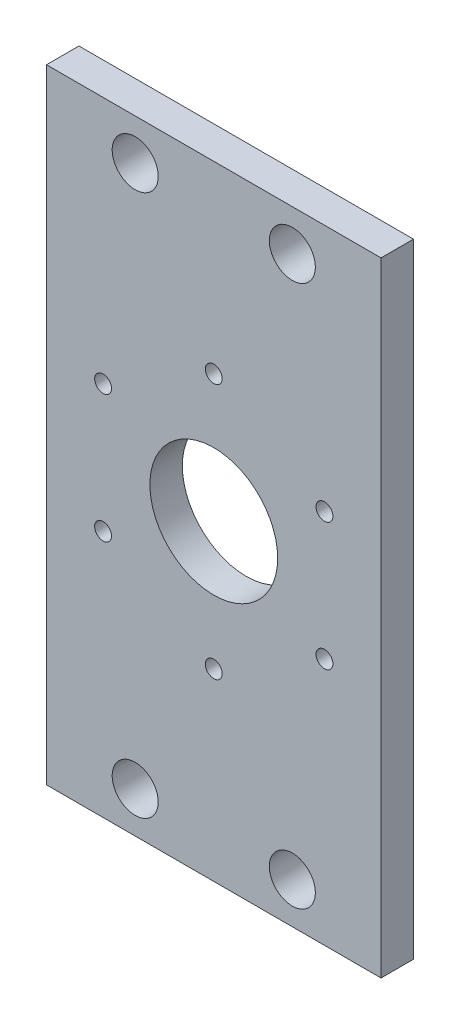
SolidWorks part; units mm, degrees
material "6061 Alloy"
ref_plane "Front Plane" through (0, 0, 0) normal (0, 0, 1) x (1, 0, 0)
ref_plane "Top Plane" through (0, 0, 0) normal (0, 1, 0) x (1, 0, 0)
ref_plane "Right Plane" through (0, 0, 0) normal (1, 0, 0) x (0, 0, -1)
sketch "Sketch1" plane through (0, 0, 0) normal (0, 0, 1) x (1, 0, 0)
  line L1 (-32.72, -61) -> (32.72, -61)
  line L2 (-32.72, -61) -> (-32.72, 61)
  line L3 (-32.72, 61) -> (32.72, 61)
  line L4 (32.72, -61) -> (32.72, 61)
  line L5 (-32.72, -61) -> (32.72, 61) construction
  line L6 (-32.72, 61) -> (32.72, -61) construction
  point P0 (0, 0)
  dimension "D1" = 122
  dimension "D2" = 65.44
extrude "Boss-Extrude1" add sketch "Sketch1" along normal blind 6.35
sketch "Sketch2" plane through (0, 0, 6.35) normal (0, 0, 1) x (1, 0, 0)
  line L0 (0, 0) -> (32.72, 0) construction
  line L1 (32.72, -61) -> (32.72, 61) construction
  line L2 (0, 0) -> (0, 61) construction
  line L3 (32.72, 61) -> (-32.72, 61) construction
  circle A0 centre (0, 0) radius 25
  point P3 (0, 25)
  point P4 (21.6506, 12.5)
  point P7 (21.6506, -12.5)
  point P8 (0, -25)
  point P9 (-21.6506, -12.5)
  point P10 (-21.6506, 12.5)
  point P15 (-15.37, 53)
  point P17 (15.37, 53)
  point P18 (15.37, -53)
  point P19 (-15.37, -53)
  dimension "D1" = 25
  dimension "D3" = 8
  dimension "D4" = 15.37
  dimension "D2" = 6
hole_wizard "M4x0.7 Tapped Hole1" positions "Sketch10" profile "Sketch11" tap size "M4x0.7" standard "ANSI Metric" end condition up to next
sketch "Sketch10" plane through (0, 0, 6.35) normal (0, 0, 1) x (1, 0, 0)
  point P0 (0, 25)
  point P3 (-21.6506, 12.5)
  point P6 (-21.6506, -12.5)
  point P9 (0, -25)
  point P12 (21.6506, -12.5)
  point P15 (21.6506, 12.5)
sketch "Sketch11" plane through (0, 25, 6.35) normal (1, 0, 0) x (0, -1, 0)
  line L0 (0, 0) -> (0, 6.35)
  line L1 (0, 6.35) -> (1.65, 6.35)
  line L2 (1.65, 6.35) -> (1.65, 0)
  line L5 (1.65, 0) -> (0, 0)
  line L11 (0, -6.35) -> (0, 107.95) construction
  dimension "Thru Tap Drill Dia." = 3.3
  dimension "Thru Tap Drill Depth" = 6.35
cosmetic thread "Hole Thread1" parameters "D2"=4
cosmetic thread "Hole Thread2" parameters "D2"=4
cosmetic thread "Hole Thread3" parameters "D2"=4
cosmetic thread "Hole Thread4" parameters "D2"=4
cosmetic thread "Hole Thread5" parameters "D2"=4
cosmetic thread "Hole Thread6" parameters "D2"=4
hole_wizard "M8 Clearance Hole1" positions "Sketch12" profile "Sketch13" hole size "M8" standard "ANSI Metric" end condition up to next
sketch "Sketch12" plane through (0, 0, 6.35) normal (0, 0, 1) x (1, 0, 0)
  point P0 (-15.37, 53)
  point P3 (15.37, 53)
  point P6 (15.37, -53)
  point P9 (-15.37, -53)
sketch "Sketch13" plane through (-15.37, 53, 6.35) normal (1, 0, 0) x (0, -1, 0)
  line L0 (0, 0) -> (0, 6.35)
  line L1 (0, 6.35) -> (4.5, 6.35)
  line L2 (4.5, 6.35) -> (4.5, 0)
  line L5 (4.5, 0) -> (0, 0)
  line L11 (0, -6.35) -> (0, 107.95) construction
  dimension "Thru Hole Dia." = 9
  dimension "Thru Hole Depth" = 6.35
sketch "Sketch14" plane through (0, 0, 6.35) normal (0, 0, 1) x (1, 0, 0)
  circle A0 centre (0, 0) radius 12.5
  dimension "D1" = 25
extrude "Cut-Extrude2" cut sketch "Sketch14" against normal up to next
